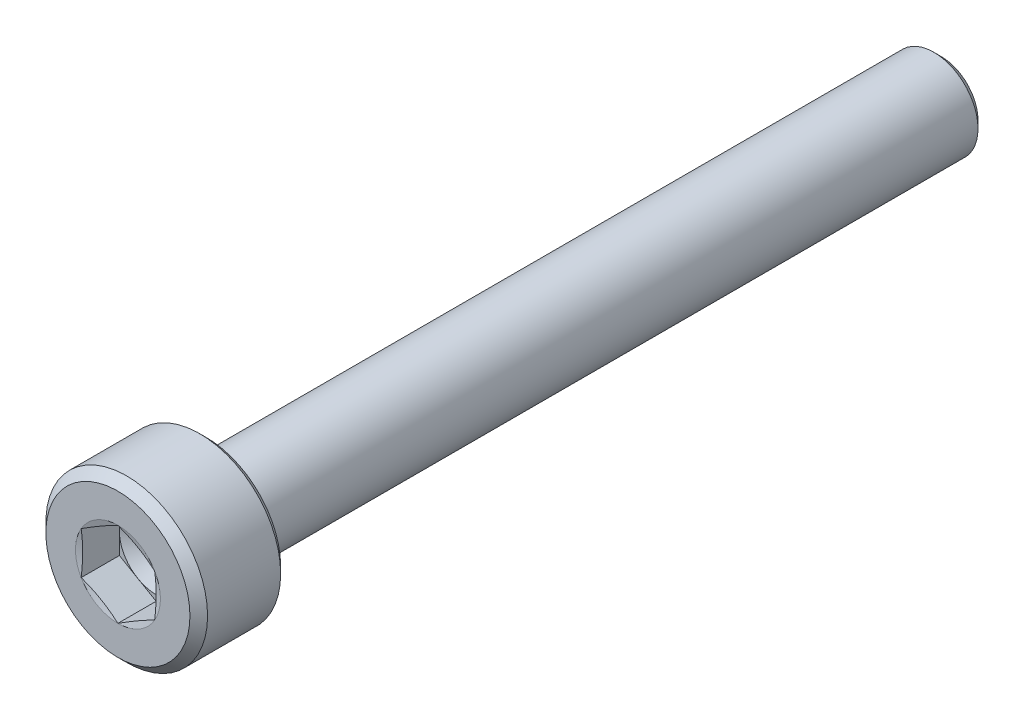
SolidWorks part; units mm, degrees
ref_plane "Front Plane" through (0, 0, 0) normal (0, 0, 1) x (1, 0, 0)
ref_plane "Top Plane" through (0, 0, 0) normal (0, 1, 0) x (1, 0, 0)
ref_plane "Right Plane" through (0, 0, 0) normal (1, 0, 0) x (0, 0, -1)
sketch "Sketch1" plane through (0, 0, 0) normal (1, 0, 0) x (0, 0, -1)
  line L0 (0, 0) -> (12.9407, 0) construction
  line L1 (0, 0) -> (0, 2.45)
  line L2 (0, 2.45) -> (0.3, 2.75)
  line L3 (0.3, 2.75) -> (2.785, 2.75)
  line L4 (3, 2.535) -> (3, 1.8)
  line L5 (3.51, 1.5) -> (27.75, 1.5)
  line L6 (27.75, 1.5) -> (28, 1.25)
  line L7 (28, 1.25) -> (28, 0)
  line L8 (28, 0) -> (0, 0)
  line L9 (2.785, 2.75) -> (3, 2.535)
  line L10 (3.4662, 1.5101) -> (3.0562, 1.7101)
  arc A2 (3.51, 1.5) -> (3.4662, 1.5101) centre (3.51, 1.6) cw
  arc A3 (3.0562, 1.7101) -> (3, 1.8) centre (3.1, 1.8) cw
  point P6 (3, 2.75)
  dimension "R2" = 0.1
  dimension "R1" = 0.1
  dimension "D1" = 45
  dimension "DK" = 5.5
  dimension "D3" = 45
  dimension "length" = 25
  dimension "K" = 3
  dimension "V" = 0.3
  dimension "HOLESIZE" = 3
  dimension "D4" = 2.5
  dimension "D5" = 45
  dimension "DW" = 5.07
  dimension "F" = 0.51
  dimension "DA" = 3.6
revolve "Revolve1" add sketch "Sketch1" angle 360 about L0
cosmetic thread "Cosmetic Thread1" parameters "D1"=18, "D2"=3
sketch "Sketch2" plane through (0, 0, 0) normal (0, 0, 1) x (1, 0, 0)
  line L0 (0, 0) -> (0, 1.4434) construction
  line L2 (0, 1.4434) -> (-1.25, 0.7217)
  line L3 (-1.25, 0.7217) -> (-1.25, -0.7217)
  line L4 (-1.25, -0.7217) -> (0, -1.4434)
  line L5 (0, -1.4434) -> (1.25, -0.7217)
  line L6 (1.25, -0.7217) -> (1.25, 0.7217)
  line L7 (1.25, 0.7217) -> (0, 1.4434)
  circle A0 centre (0, 0) radius 1.25 construction
  dimension "S" = 2.5
extrude "Cut-Extrude1" cut sketch "Sketch2" against normal blind 1.3
sketch "Sketch3" plane through (0, 0, 0) normal (1, 0, 0) x (0, 0, -1)
  line L0 (1.3, 0) -> (28, 0) construction
  line L1 (28, -1.25) -> (28, 1.25) construction
  line L2 (1.3, 0) -> (1.3, 1.25)
  line L4 (1.3, 1.25) -> (2.0217, 0)
  line L5 (2.0217, 0) -> (1.3, 0)
  line L6 (0, 2.45) -> (0, -2.45) construction
  dimension "DRILLANG" = 60
  dimension "DRILL DEPTH" = 1.3
  dimension "S2" = 2.5
revolve "Cut-Revolve2" cut sketch "Sketch3" angle 360 about L0
sketch "Sketch4" plane through (0, 0, 0) normal (1, 0, 0) x (0, 0, -1)
  line L0 (0, 0) -> (4.6121, 0) construction
  line L1 (0, 1.4434) -> (0, 1.25)
  line L2 (0, 2.45) -> (0, -2.45) construction
  line L3 (0, 1.25) -> (0.0518, 1.25)
  line L4 (0.0518, 1.25) -> (0, 1.4434)
  point P12 (0.0259, 1.25)
  dimension "D1" = 2.5
  dimension "D2" = 15
revolve "Cut-Revolve3" cut sketch "Sketch4" angle 360 about L0
